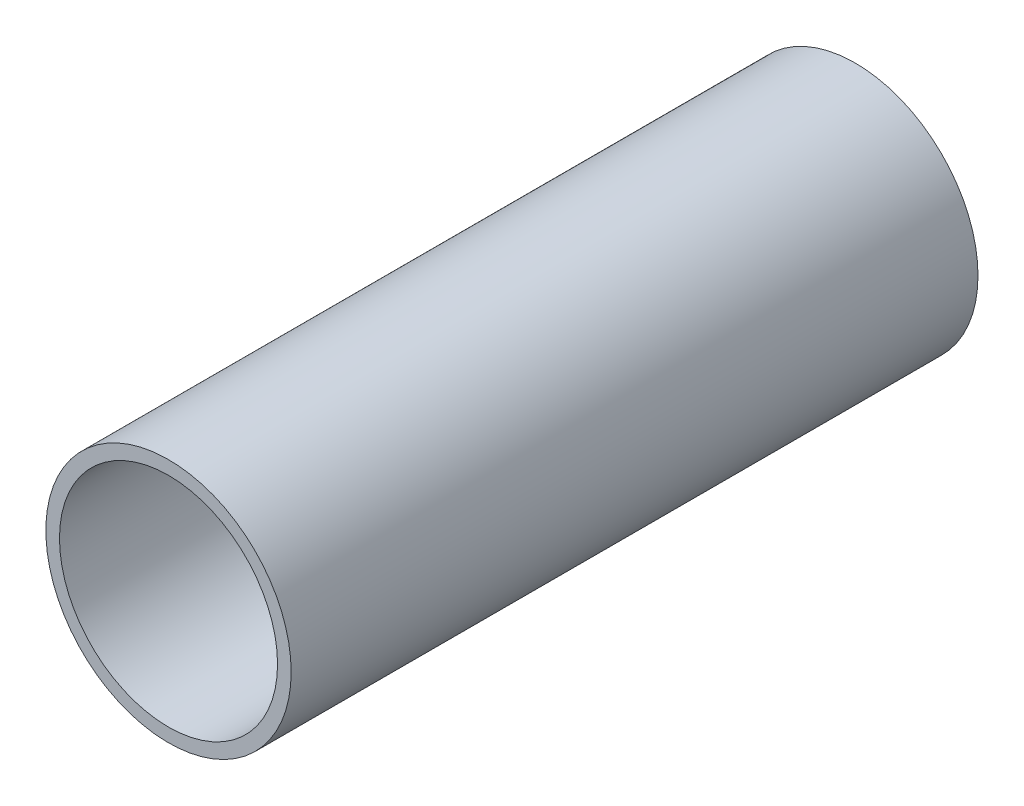
SolidWorks part; units mm, degrees
material "ABS PC"
ref_plane "Front Plane" through (0, 0, 0) normal (0, 0, 1) x (1, 0, 0)
ref_plane "Top Plane" through (0, 0, 0) normal (0, 1, 0) x (1, 0, 0)
ref_plane "Right Plane" through (0, 0, 0) normal (1, 0, 0) x (0, 0, -1)
sketch "Sketch1" plane through (0, 0, 0) normal (0, 0, 1) x (1, 0, 0)
  circle A0 centre (0, 0) radius 28.575
  circle A1 centre (0, 0) radius 25.4
  dimension "D1" = 57.15
  dimension "D2" = 50.8
extrude "Boss-Extrude1" add sketch "Sketch1" along normal mid plane 160
